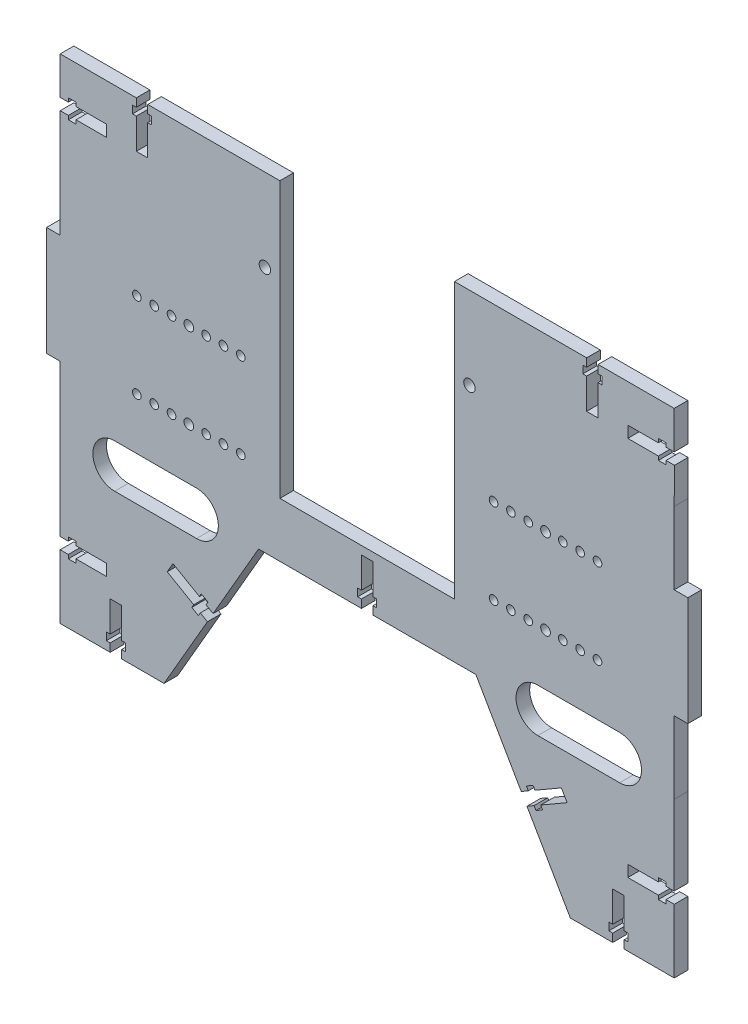
SolidWorks part; units mm, degrees
ref_plane "Front Plane" through (0, 0, 0) normal (0, 0, 1) x (1, 0, 0)
ref_plane "Top Plane" through (0, 0, 0) normal (0, 1, 0) x (1, 0, 0)
ref_plane "Right Plane" through (0, 0, 0) normal (1, 0, 0) x (0, 0, -1)
sketch "Sketch1" plane through (0, 0, 0) normal (0, 0, 1) x (1, 0, 0)
  line L0 (39.458, -28.3332) -> (72.458, -28.3332)
  line L1 (39.458, 51.6668) -> (39.458, -28.3332)
  line L2 (72.458, 51.6668) -> (39.458, 51.6668)
  line L3 (72.458, -28.3332) -> (72.458, 51.6668)
  line L4 (-73.542, -28.3332) -> (-40.542, -28.3332)
  line L5 (-73.542, 51.6668) -> (-73.542, -28.3332)
  line L6 (-40.542, 51.6668) -> (-73.542, 51.6668)
  line L7 (117.028, -95.8332) -> (117.028, -34.826)
  line L8 (117.028, -34.826) -> (112.428, -34.826)
  line L9 (107.428, -29.826) -> (107.428, 53.1596)
  line L10 (112.428, 58.1596) -> (117.0267, 58.1596)
  line L11 (117.0267, 58.1596) -> (117.0263, 74.955)
  line L12 (117.0263, 74.955) -> (117.0093, 95.0203)
  line L13 (117.0093, 95.0203) -> (36.109, 95.0203)
  line L14 (-37.1929, 95.0203) -> (-118.0932, 95.0203)
  line L15 (-118.0932, 95.0203) -> (-118.1103, 74.955)
  line L16 (-118.1103, 74.955) -> (-118.1106, 58.1596)
  line L17 (-118.1106, 58.1596) -> (-113.512, 58.1596)
  line L18 (-108.512, 53.1596) -> (-108.512, -29.826)
  line L19 (-113.512, -34.826) -> (-118.112, -34.826)
  line L20 (-118.112, -34.826) -> (-118.112, -95.8332)
  line L21 (-118.112, -95.8332) -> (-72.1334, -95.8332)
  line L22 (-72.1334, -95.8332) -> (-37.4924, -35.8332)
  line L23 (-37.4924, -35.8332) -> (36.4085, -35.8332)
  line L24 (36.4085, -35.8332) -> (71.0495, -95.8332)
  line L25 (71.0495, -95.8332) -> (117.028, -95.8332)
  line L26 (-40.542, -28.3332) -> (-40.542, 51.6668)
  circle A0 centre (-93.742, 37.1668) radius 2.5
  circle A1 centre (-93.742, -13.8332) radius 2.5
  arc A2 (107.428, -29.826) -> (112.428, -34.826) centre (112.428, -29.826) ccw
  arc A3 (112.428, 58.1596) -> (107.428, 53.1596) centre (112.428, 53.1596) ccw
  arc A4 (-37.1929, 95.0203) -> (36.109, 95.0203) centre (-0.542, 160.455) ccw
  arc A5 (-108.512, 53.1596) -> (-113.512, 58.1596) centre (-113.512, 53.1596) ccw
  arc A6 (-113.512, -34.826) -> (-108.512, -29.826) centre (-113.512, -29.826) ccw
  circle A7 centre (92.658, -13.8332) radius 2.5
  circle A8 centre (92.658, 37.1668) radius 2.5
  circle A9 centre (35.458, 29.1668) radius 2
  circle A10 centre (35.458, -5.8332) radius 2
  circle A11 centre (4.458, -5.8332) radius 2
  circle A12 centre (-5.542, -5.8332) radius 2
  circle A13 centre (-36.542, -5.8332) radius 2
  circle A14 centre (-36.542, 29.1668) radius 2
  circle A15 centre (4.458, 29.1668) radius 2
  circle A16 centre (-5.542, 29.1668) radius 2
  circle A17 centre (25.9225, 60.9906) radius 1.6
  circle A18 centre (25.9225, 81.9195) radius 1.6
  circle A19 centre (-27.0064, 81.9195) radius 1.6
  circle A20 centre (-27.0064, 60.9906) radius 1.6
extrude "Boss-Extrude1" add sketch "Sketch1" along normal blind 5
sketch "Sketch2" plane through (0, 0, 5) normal (0, 0, 1) x (1, 0, 0)
  line L4 (72.458, 51.6668) -> (39.458, 51.6668)
  line L5 (72.458, -28.3332) -> (72.458, 51.6668)
  line L6 (39.458, -28.3332) -> (72.458, -28.3332)
  line L7 (39.458, 51.6668) -> (39.458, -28.3332)
  line L8 (72.458, 51.6668) -> (39.458, 51.6668)
  line L9 (72.458, -28.3332) -> (72.458, 51.6668)
  line L10 (39.458, -28.3332) -> (72.458, -28.3332)
  line L11 (39.458, 51.6668) -> (39.458, -28.3332)
  line L12 (-40.542, 51.6668) -> (-73.542, 51.6668)
  line L13 (-40.542, -28.3332) -> (-40.542, 51.6668)
  line L14 (-73.542, -28.3332) -> (-40.542, -28.3332)
  line L15 (-73.542, 51.6668) -> (-73.542, -28.3332)
  line L16 (-40.542, 51.6668) -> (-73.542, 51.6668)
  line L17 (-40.542, -28.3332) -> (-40.542, 51.6668)
  line L18 (-73.542, -28.3332) -> (-40.542, -28.3332)
  line L19 (-73.542, 51.6668) -> (-73.542, -28.3332)
  dimension "D1" = 0
  dimension "D2" = 0
extrude "Boss-Extrude2" add sketch "Sketch2" against normal blind 5
sketch "Sketch3" plane through (0, 0, 5) normal (0, 0, 1) x (1, 0, 0)
  line L0 (31.458, 33.4416) -> (31.458, -11.5584) construction
  line L1 (8.458, -11.5584) -> (8.458, 33.4416) construction
  line L2 (-9.542, 33.4416) -> (-9.542, -11.5584) construction
  line L3 (-32.542, -11.5584) -> (-32.542, 33.4416) construction
  line L4 (31.458, 33.4416) -> (31.458, -11.5584)
  line L5 (8.458, -11.5584) -> (8.458, 33.4416)
  line L6 (-9.542, 33.4416) -> (-9.542, -11.5584)
  line L7 (-32.542, -11.5584) -> (-32.542, 33.4416)
  line L8 (-32.542, -11.5584) -> (-9.542, -11.5584)
  line L9 (-32.542, 33.4416) -> (-9.542, 33.4416)
  line L10 (8.458, 33.4416) -> (31.458, 33.4416)
  line L11 (8.458, -11.5584) -> (31.458, -11.5584)
extrude "Cut-Extrude3" cut sketch "Sketch3" against normal blind 5
sketch "Sketch4" plane through (0, 0, 5) normal (0, 0, 1) x (1, 0, 0)
  circle A1 centre (92.658, -13.8332) radius 2.5
  circle A2 centre (92.658, -13.8332) radius 2.5
  circle A3 centre (92.658, 37.1668) radius 2.5
  circle A4 centre (92.658, 37.1668) radius 2.5
  circle A5 centre (35.458, -5.8332) radius 2
  circle A6 centre (35.458, -5.8332) radius 2
  circle A7 centre (35.458, 29.1668) radius 2
  circle A8 centre (35.458, 29.1668) radius 2
  circle A9 centre (4.458, -5.8332) radius 2
  circle A10 centre (4.458, -5.8332) radius 2
  circle A11 centre (4.458, 29.1668) radius 2
  circle A12 centre (4.458, 29.1668) radius 2
  circle A13 centre (-5.542, -5.8332) radius 2
  circle A14 centre (-5.542, -5.8332) radius 2
  circle A15 centre (-5.542, 29.1668) radius 2
  circle A16 centre (-5.542, 29.1668) radius 2
  circle A17 centre (-36.542, -5.8332) radius 2
  circle A18 centre (-36.542, -5.8332) radius 2
  circle A19 centre (-36.542, 29.1668) radius 2
  circle A20 centre (-36.542, 29.1668) radius 2
  circle A21 centre (-93.742, -13.8332) radius 2.5
  circle A22 centre (-93.742, -13.8332) radius 2.5
  circle A23 centre (-93.742, 37.1668) radius 2.5
  circle A24 centre (-93.742, 37.1668) radius 2.5
  circle A25 centre (25.9225, 60.9906) radius 1.6
  circle A26 centre (25.9225, 60.9906) radius 1.6
  circle A27 centre (25.9225, 81.9195) radius 1.6
  circle A28 centre (25.9225, 81.9195) radius 1.6
  circle A29 centre (-27.0064, 81.9195) radius 1.6
  circle A30 centre (-27.0064, 81.9195) radius 1.6
  circle A31 centre (-27.0064, 60.9906) radius 1.6
  circle A32 centre (-27.0064, 60.9906) radius 1.6
  dimension "D1" = 0
  dimension "D2" = 0
  dimension "D3" = 0
  dimension "D4" = 0
  dimension "D5" = 0
  dimension "D6" = 0
  dimension "D7" = 0
  dimension "D8" = 0
  dimension "D9" = 0
  dimension "D10" = 0
  dimension "D11" = 0
  dimension "D12" = 0
  dimension "D13" = 0
  dimension "D14" = 0
  dimension "D15" = 0
  dimension "D16" = 0
extrude "Boss-Extrude3" add sketch "Sketch4" against normal blind 5
sketch "Sketch5" plane through (0, 0, 5) normal (0, 0, 1) x (1, 0, 0)
  line L0 (-92.842, 10.9401) -> (-51.8932, 10.9401) construction
  line L1 (-92.842, 14.0401) -> (-92.842, 7.8401) construction
  line L2 (-0.542, -35.8332) -> (-0.542, 25.4222) construction
  line L3 (-37.4924, -35.8332) -> (36.4085, -35.8332) construction
  line L4 (91.758, 10.9401) -> (50.8093, 10.9401) construction
  circle A0 centre (-84.9795, 26.5626) radius 1.5875
  circle A1 centre (-78.6295, 26.5626) radius 1.5875
  circle A2 centre (-72.2795, 26.5626) radius 1.5875
  circle A3 centre (-65.9295, 26.5626) radius 1.7775
  circle A4 centre (-59.5795, 26.5626) radius 1.5875
  circle A5 centre (-53.2295, 26.5626) radius 1.5875
  circle A6 centre (-46.8795, 26.5626) radius 1.5875
  circle A7 centre (-46.8795, -4.6823) radius 1.5875
  circle A8 centre (-53.2295, -4.6823) radius 1.5875
  circle A9 centre (-59.5795, -4.6823) radius 1.5875
  circle A10 centre (-65.9295, -4.6823) radius 1.7775
  circle A11 centre (-72.2795, -4.6823) radius 1.5875
  circle A12 centre (-78.6295, -4.6823) radius 1.5875
  circle A13 centre (-84.9795, -4.6823) radius 1.5875
  circle A14 centre (83.8955, -4.6823) radius 1.5875
  circle A15 centre (77.5455, -4.6823) radius 1.5875
  circle A16 centre (71.1955, -4.6823) radius 1.5875
  circle A17 centre (64.8455, -4.6823) radius 1.7775
  circle A18 centre (58.4955, -4.6823) radius 1.5875
  circle A19 centre (52.1455, -4.6823) radius 1.5875
  circle A20 centre (45.7955, -4.6823) radius 1.5875
  circle A21 centre (45.7955, 26.5626) radius 1.5875
  circle A22 centre (52.1455, 26.5626) radius 1.5875
  circle A23 centre (58.4955, 26.5626) radius 1.5875
  circle A24 centre (64.8455, 26.5626) radius 1.7775
  circle A25 centre (71.1955, 26.5626) radius 1.5875
  circle A26 centre (77.5455, 26.5626) radius 1.5875
  circle A27 centre (83.8955, 26.5626) radius 1.5875
extrude "Cut-Extrude4" cut sketch "Sketch5" against normal blind 5
sketch "Sketch7" plane through (0, 0, 5) normal (0, 0, 1) x (1, 0, 0)
  line L2 (-37.1929, 89.2951) -> (-75.5429, 89.2951) construction
  line L7 (36.109, 89.2951) -> (74.459, 89.2951) construction
  line L9 (112.028, -35.5484) -> (112.028, -63.9534) construction
  line L10 (-113.112, -35.5484) -> (-113.112, -63.9534) construction
  line L15 (112.028, -91.5584) -> (93.683, -91.5584) construction
  line L18 (73.2366, -90.3465) -> (58.0376, -64.0211) construction
  line L23 (-37.4915, -31.5584) -> (-2.6415, -31.5584) construction
  line L24 (-74.3205, -90.3465) -> (-59.1215, -64.0211) construction
  line L25 (-113.112, -91.5584) -> (-94.767, -91.5584) construction
  line L27 (-113.0929, 89.2951) -> (-113.0929, 75.4651)
  line L29 (-37.1929, 89.2951) -> (-113.0929, 89.2951)
  line L30 (36.109, 89.2951) -> (112.0089, 89.2951)
  line L31 (112.0089, 89.2951) -> (112.009, 75.4651)
  line L32 (112.028, -35.5484) -> (112.028, -91.5584)
  line L33 (-113.112, -35.5484) -> (-113.112, -91.5584)
  line L34 (112.028, -91.5584) -> (73.9362, -91.5584)
  line L35 (73.2366, -90.3465) -> (58.0376, -64.0211)
  line L36 (-37.4915, -31.5584) -> (-2.6415, -31.5584)
  line L37 (-74.3205, -90.3465) -> (-59.1215, -64.0211)
  line L38 (-113.112, -91.5584) -> (-75.0201, -91.5584)
  line L39 (-74.3205, -90.3465) -> (-75.0201, -91.5584)
  line L40 (-37.4915, -31.5584) -> (-40.3791, -31.5584)
  line L41 (-59.1215, -64.0211) -> (-40.3791, -31.5584)
  line L42 (-113.112, -35.5484) -> (-118.112, -34.826)
  line L43 (-118.112, -34.826) -> (-118.112, -95.8332)
  line L44 (-118.112, -95.8332) -> (-72.1334, -95.8332)
  line L45 (-72.1334, -95.8332) -> (-37.4924, -35.8332)
  line L46 (-37.4924, -35.8332) -> (36.4085, -35.8332)
  line L47 (36.4085, -35.8332) -> (71.0495, -95.8332)
  line L48 (71.0495, -95.8332) -> (117.028, -95.8332)
  line L49 (117.028, -95.8332) -> (117.028, -34.826)
  line L50 (117.028, -34.826) -> (112.028, -35.5484)
  line L51 (-2.6415, -31.5584) -> (39.2952, -31.5584)
  line L52 (58.0376, -64.0211) -> (39.2952, -31.5584)
  line L53 (73.2366, -90.3465) -> (73.9362, -91.5584)
  line L54 (117.0267, 58.1596) -> (117.0263, 74.955) construction
  line L55 (117.0263, 74.955) -> (117.0093, 95.0203) construction
  line L56 (117.0093, 95.0203) -> (36.109, 95.0203) construction
  line L57 (-118.1106, 58.1596) -> (-113.512, 58.1596) construction
  line L58 (-118.1103, 74.955) -> (-118.1106, 58.1596) construction
  line L59 (-118.0932, 95.0203) -> (-118.1103, 74.955) construction
  line L60 (-37.1929, 95.0203) -> (-118.0932, 95.0203) construction
  line L61 (117.0267, 58.1596) -> (117.0263, 74.955)
  line L62 (117.0263, 74.955) -> (117.0093, 95.0203)
  line L63 (117.0093, 95.0203) -> (36.109, 95.0203)
  line L64 (-118.1106, 58.1596) -> (-113.512, 58.1596)
  line L65 (-118.1103, 74.955) -> (-118.1106, 58.1596)
  line L66 (-118.0932, 95.0203) -> (-118.1103, 74.955)
  line L67 (-37.1929, 95.0203) -> (-118.0932, 95.0203)
  line L68 (-37.1929, 95.0203) -> (-37.1929, 89.2951)
  line L69 (36.109, 95.0203) -> (36.109, 89.2951)
  line L70 (-113.512, 58.1596) -> (-113.0929, 75.4651)
  line L71 (117.0267, 58.1596) -> (112.009, 75.4651)
extrude "Cut-Extrude5" cut sketch "Sketch7" against normal blind 10
sketch "Sketch9" plane through (0, 0, 5) normal (0, 0, 1) x (1, 0, 0)
  line L0 (-92.667, -96.5584) -> (-92.667, -68.7145) construction
  line L1 (-97.667, -96.5584) -> (-87.667, -96.5584) construction
  line L2 (-118.112, -66.0534) -> (-90.5831, -66.0534) construction
  line L3 (-118.112, -61.0534) -> (-118.112, -71.0534) construction
  line L4 (-53.7414, -64.7025) -> (-78.8211, -50.2227) construction
  line L5 (-56.2414, -69.0326) -> (-51.2414, -60.3723) construction
  line L6 (-107.2929, 71.2651) -> (-96.0929, 71.2651)
  line L8 (-107.2929, 69.8651) -> (-107.2929, 71.2651)
  line L21 (-110.0929, 69.8651) -> (-107.2929, 69.8651)
  line L34 (-110.0929, 71.2651) -> (-110.0929, 69.8651)
  line L47 (-113.0929, 71.2651) -> (-110.0929, 71.2651)
  line L60 (-77.6429, 89.2951) -> (-79.7429, 89.2951)
  line L65 (-113.0929, 89.2951) -> (-37.1929, 89.2951) construction
  line L78 (-79.7429, 89.2951) -> (-79.7429, 86.2951)
  line L90 (-0.5415, -36.5584) -> (-0.5415, -3.9222) construction
  line L91 (-5.5415, -36.5584) -> (4.4585, -36.5584) construction
  line L92 (-118.0929, 73.3651) -> (-88.4214, 73.3651) construction
  line L94 (-77.6429, 94.2951) -> (-77.6429, 80.7077) construction
  line L159 (-79.7429, 86.2951) -> (-81.1429, 86.2951)
  line L160 (-90.567, -91.5584) -> (-94.767, -91.5584)
  line L161 (-81.1429, 86.2951) -> (-81.1429, 83.4951)
  line L162 (-75.0201, -91.5584) -> (-113.112, -91.5584) construction
  line L163 (-94.767, -91.5584) -> (-94.767, -88.5584)
  line L164 (-94.767, -88.5584) -> (-96.167, -88.5584)
  line L165 (-96.167, -88.5584) -> (-96.167, -85.7584)
  line L166 (-96.167, -85.7584) -> (-94.767, -85.7584)
  line L167 (-94.767, -85.7584) -> (-94.767, -74.5584)
  line L168 (-94.767, -74.5584) -> (-90.567, -74.5584)
  line L169 (-113.112, -68.1534) -> (-113.112, -63.9534)
  line L170 (-113.112, -91.5584) -> (-113.112, -35.5484) construction
  line L171 (-113.112, -63.9534) -> (-110.112, -63.9534)
  line L172 (-110.112, -63.9534) -> (-110.112, -62.5534)
  line L173 (-110.112, -62.5534) -> (-107.312, -62.5534)
  line L174 (-107.312, -62.5534) -> (-107.312, -63.9534)
  line L175 (-107.312, -63.9534) -> (-96.112, -63.9534)
  line L176 (-96.112, -63.9534) -> (-96.112, -68.1534)
  line L177 (-57.0215, -60.3838) -> (-59.1215, -64.0211)
  line L178 (-40.3791, -31.5584) -> (-75.0201, -91.5584) construction
  line L179 (-59.1215, -64.0211) -> (-61.7196, -62.5211)
  line L180 (-61.7196, -62.5211) -> (-62.4196, -63.7335)
  line L181 (-62.4196, -63.7335) -> (-64.8444, -62.3335)
  line L182 (-64.8444, -62.3335) -> (-64.1444, -61.1211)
  line L183 (-64.1444, -61.1211) -> (-73.8439, -55.5211)
  line L184 (-73.8439, -55.5211) -> (-71.7439, -51.8838)
  line L185 (-107.312, -68.1534) -> (-96.112, -68.1534)
  line L186 (-107.312, -69.5534) -> (-107.312, -68.1534)
  line L187 (-110.112, -69.5534) -> (-107.312, -69.5534)
  line L188 (-110.112, -68.1534) -> (-110.112, -69.5534)
  line L189 (-113.112, -68.1534) -> (-110.112, -68.1534)
  line L190 (-90.567, -85.7584) -> (-90.567, -74.5584)
  line L191 (-89.167, -85.7584) -> (-90.567, -85.7584)
  line L192 (-89.167, -88.5584) -> (-89.167, -85.7584)
  line L193 (-90.567, -88.5584) -> (-89.167, -88.5584)
  line L194 (-90.567, -91.5584) -> (-90.567, -88.5584)
  line L195 (-62.0444, -57.4838) -> (-71.7439, -51.8838)
  line L196 (-61.3444, -56.2714) -> (-62.0444, -57.4838)
  line L197 (-58.9196, -57.6714) -> (-61.3444, -56.2714)
  line L198 (-59.6196, -58.8838) -> (-58.9196, -57.6714)
  line L199 (-57.0215, -60.3838) -> (-59.6196, -58.8838)
  line L202 (-113.0929, 75.4651) -> (-110.0929, 75.4651)
  line L203 (-110.0929, 75.4651) -> (-110.0929, 76.8651)
  line L204 (-110.0929, 76.8651) -> (-107.2929, 76.8651)
  line L205 (-107.2929, 76.8651) -> (-107.2929, 75.4651)
  line L206 (-107.2929, 75.4651) -> (-96.0929, 75.4651)
  line L207 (-96.0929, 75.4651) -> (-96.0929, 71.2651)
  line L208 (-81.1429, 83.4951) -> (-79.7429, 83.4951)
  line L209 (-79.7429, 83.4951) -> (-79.7429, 72.2951)
  line L210 (-79.7429, 72.2951) -> (-75.5429, 72.2951)
  line L211 (-75.5429, 83.4951) -> (-75.5429, 72.2951)
  line L212 (-74.1429, 83.4951) -> (-75.5429, 83.4951)
  line L213 (-74.1429, 86.2951) -> (-74.1429, 83.4951)
  line L214 (-75.5429, 86.2951) -> (-74.1429, 86.2951)
  line L215 (-75.5429, 89.2951) -> (-75.5429, 86.2951)
  line L216 (-77.6429, 89.2951) -> (-75.5429, 89.2951)
  line L217 (76.5598, 94.2951) -> (76.5598, 80.7077) construction
  line L218 (117.0098, 73.3651) -> (87.3384, 73.3651) construction
  line L219 (52.6583, -64.7025) -> (77.738, -50.2227) construction
  line L220 (117.0289, -66.0534) -> (89.5, -66.0534) construction
  line L221 (91.5839, -96.5584) -> (91.5839, -68.7145) construction
  line L222 (76.5598, 89.2951) -> (74.4598, 89.2951)
  line L223 (74.4598, 89.2951) -> (74.4598, 86.2951)
  line L224 (74.4598, 86.2951) -> (73.0598, 86.2951)
  line L225 (73.0598, 86.2951) -> (73.0598, 83.4951)
  line L226 (73.0598, 83.4951) -> (74.4598, 83.4951)
  line L227 (74.4598, 83.4951) -> (74.4598, 72.2951)
  line L228 (78.6598, 72.2951) -> (74.4598, 72.2951)
  line L229 (78.6598, 83.4951) -> (78.6598, 72.2951)
  line L230 (80.0598, 83.4951) -> (78.6598, 83.4951)
  line L231 (95.0098, 75.4651) -> (95.0098, 71.2651)
  line L232 (106.2098, 75.4651) -> (95.0098, 75.4651)
  line L233 (106.2098, 76.8651) -> (106.2098, 75.4651)
  line L234 (109.0098, 76.8651) -> (106.2098, 76.8651)
  line L235 (109.0098, 75.4651) -> (109.0098, 76.8651)
  line L236 (112.0098, 75.4651) -> (109.0098, 75.4651)
  line L237 (112.0098, 75.4622) -> (112.0098, 75.4651)
  line L238 (55.9384, -60.3838) -> (58.5365, -58.8838)
  line L239 (58.5365, -58.8838) -> (57.8365, -57.6714)
  line L240 (57.8365, -57.6714) -> (60.2614, -56.2714)
  line L241 (60.2614, -56.2714) -> (60.9614, -57.4838)
  line L242 (60.9614, -57.4838) -> (70.6609, -51.8838)
  line L243 (89.4839, -91.5584) -> (89.4839, -88.5584)
  line L244 (89.4839, -88.5584) -> (88.0839, -88.5584)
  line L245 (88.0839, -88.5584) -> (88.0839, -85.7584)
  line L246 (88.0839, -85.7584) -> (89.4839, -85.7584)
  line L247 (89.4839, -85.7584) -> (89.4839, -74.5584)
  line L248 (112.0289, -68.1534) -> (109.0289, -68.1534)
  line L249 (109.0289, -68.1534) -> (109.0289, -69.5534)
  line L250 (109.0289, -69.5534) -> (106.2289, -69.5534)
  line L251 (106.2289, -69.5534) -> (106.2289, -68.1534)
  line L252 (106.2289, -68.1534) -> (95.0289, -68.1534)
  line L253 (72.7609, -55.5211) -> (70.6609, -51.8838)
  line L254 (63.0614, -61.1211) -> (72.7609, -55.5211)
  line L255 (63.7614, -62.3335) -> (63.0614, -61.1211)
  line L256 (61.3365, -63.7335) -> (63.7614, -62.3335)
  line L257 (60.6365, -62.5211) -> (61.3365, -63.7335)
  line L258 (58.0384, -64.0211) -> (60.6365, -62.5211)
  line L259 (55.9384, -60.3838) -> (58.0384, -64.0211)
  line L260 (95.0289, -63.9534) -> (95.0289, -68.1534)
  line L261 (106.2289, -63.9534) -> (95.0289, -63.9534)
  line L262 (106.2289, -62.5534) -> (106.2289, -63.9534)
  line L263 (109.0289, -62.5534) -> (106.2289, -62.5534)
  line L264 (109.0289, -63.9534) -> (109.0289, -62.5534)
  line L265 (112.0289, -63.9534) -> (109.0289, -63.9534)
  line L266 (112.0289, -68.1534) -> (112.0289, -63.9534)
  line L267 (93.6839, -74.5584) -> (89.4839, -74.5584)
  line L268 (93.6839, -85.7584) -> (93.6839, -74.5584)
  line L269 (95.0839, -85.7584) -> (93.6839, -85.7584)
  line L270 (95.0839, -88.5584) -> (95.0839, -85.7584)
  line L271 (93.6839, -88.5584) -> (95.0839, -88.5584)
  line L272 (93.6839, -91.5584) -> (93.6839, -88.5584)
  line L273 (80.0598, 86.2951) -> (80.0598, 83.4951)
  line L274 (89.4839, -91.5584) -> (93.6839, -91.5584)
  line L275 (78.6598, 86.2951) -> (80.0598, 86.2951)
  line L276 (78.6598, 89.2951) -> (78.6598, 86.2951)
  line L277 (76.5598, 89.2951) -> (78.6598, 89.2951)
  line L278 (112.0098, 71.2651) -> (109.0098, 71.2651)
  line L279 (109.0098, 71.2651) -> (109.0098, 69.8651)
  line L280 (109.0098, 69.8651) -> (106.2098, 69.8651)
  line L281 (106.2098, 69.8651) -> (106.2098, 71.2651)
  line L282 (106.2098, 71.2651) -> (95.0098, 71.2651)
  line L283 (117.028, -34.826) -> (112.028, -35.5484) construction
  line L284 (117.028, -34.826) -> (112.428, -34.826) construction
  line L285 (117.028, -34.826) -> (112.028, -35.5484)
  line L286 (117.028, -34.826) -> (112.428, -34.826)
  line L287 (112.028, -35.5484) -> (112.028, -34.81)
  line L288 (-113.1111, -35.5484) -> (-113.1111, -34.81)
  line L289 (-118.1111, -34.826) -> (-113.5111, -34.826)
  line L290 (-118.1111, -34.826) -> (-113.1111, -35.5484)
  line L291 (-113.0929, 71.2651) -> (-113.0929, 58.142)
  line L294 (-113.512, 58.1596) -> (-113.0929, 75.4651)
  line L295 (-113.0929, 71.2651) -> (-113.1946, 71.2651)
  line L296 (-113.0929, 73.3651) -> (-113.1437, 73.3651)
  line L297 (117.0098, 73.3651) -> (87.3384, 73.3651) construction
  line L298 (112.0098, 73.3651) -> (112.0607, 73.3651)
  line L299 (112.0098, 71.2651) -> (112.1115, 71.2651)
  line L300 (112.0098, 71.2651) -> (112.0098, 58.142)
  line L301 (112.0098, 71.2651) -> (109.0098, 71.2651)
  line L302 (109.0098, 71.2651) -> (109.0098, 69.8651)
  line L303 (109.0098, 69.8651) -> (106.2098, 69.8651)
  line L304 (106.2098, 69.8651) -> (106.2098, 71.2651)
  line L305 (106.2098, 71.2651) -> (95.0098, 71.2651)
  line L306 (-2.6415, -31.5584) -> (-2.6415, -28.5584)
  line L307 (39.2952, -31.5584) -> (-40.3791, -31.5584) construction
  line L308 (-2.6415, -28.5584) -> (-4.0415, -28.5584)
  line L309 (-4.0415, -28.5584) -> (-4.0415, -25.7584)
  line L310 (-4.0415, -25.7584) -> (-2.6415, -25.7584)
  line L311 (-2.6415, -25.7584) -> (-2.6415, -14.5584)
  line L312 (-2.6415, -14.5584) -> (1.5585, -14.5584)
  line L313 (-2.6415, -31.5584) -> (-0.542, -31.5584)
  line L314 (1.5585, -31.5584) -> (-0.5411, -31.5584)
  line L315 (1.5585, -25.7584) -> (1.5585, -14.5584)
  line L316 (2.9585, -25.7584) -> (1.5585, -25.7584)
  line L317 (2.9585, -28.5584) -> (2.9585, -25.7584)
  line L318 (1.5585, -28.5584) -> (2.9585, -28.5584)
  line L319 (1.5585, -31.5584) -> (1.5585, -28.5584)
  line L320 (112.009, 75.4651) -> (117.0267, 58.1596) construction
  line L321 (112.428, 58.1596) -> (117.0267, 58.1596) construction
  line L322 (112.009, 75.4651) -> (117.0267, 58.1596)
  line L323 (112.428, 58.1596) -> (117.0267, 58.1596)
  line L324 (112.0098, 58.142) -> (112.1115, 71.2651)
  arc A0 (107.428, -29.826) -> (112.428, -34.826) centre (112.428, -29.826) ccw construction
  arc A1 (112.028, -34.81) -> (112.428, -34.826) centre (112.428, -29.826) ccw
  arc A2 (-113.1111, -34.81) -> (-113.5111, -34.826) centre (-113.5111, -29.826) cw
  arc A3 (-108.512, 53.1596) -> (-113.512, 58.1596) centre (-113.512, 53.1596) ccw construction
  arc A4 (-113.0929, 58.142) -> (-113.512, 58.1596) centre (-113.512, 53.1596) ccw
  arc A5 (112.0098, 58.142) -> (112.4289, 58.1596) centre (112.4289, 53.1596) cw
  point P8 (-96.0929, 73.3651)
  point P60 (-96.112, -66.0534)
  point P65 (-113.112, -66.0534)
  point P66 (-92.667, -74.5584)
  point P71 (-92.667, -91.5584)
  point P72 (-72.7939, -53.7025)
  point P77 (-58.0715, -62.2025)
  point P88 (-113.0929, 73.3651)
  point P99 (-77.6429, 72.2951)
  point P175 (76.5598, 72.2951)
  point P176 (112.0098, 73.3651)
  point P177 (56.9884, -62.2025)
  point P178 (71.7109, -53.7025)
  point P179 (91.5839, -91.5584)
  point P180 (91.5839, -74.5584)
  point P181 (112.0289, -66.0534)
  point P182 (95.0289, -66.0534)
  point P183 (95.0098, 73.3651)
  point P211 (112.0098, 73.3651)
  point P230 (-0.5415, -14.5584)
  dimension "D1" = 2.1
  dimension "D2" = 2.1
  dimension "D3" = 3.5
  dimension "D4" = 2.8
  dimension "D5" = 3
  dimension "D6" = 17
  dimension "D7" = 4.2
  dimension "D8" = 4.2
  dimension "D9" = 7
  dimension "D10" = 17
  dimension "D11" = 2.8
  dimension "D12" = 3
  dimension "D13" = 3
  dimension "D14" = 2.1
  dimension "D15" = 2.1
  dimension "D16" = 3.5
  dimension "D17" = 2.8
  dimension "D18" = 17
  dimension "D20" = 2.1
  dimension "D21" = 3.5
  dimension "D23" = 2.8
  dimension "D24" = 4.2
  dimension "D25" = 2.1
  dimension "D26" = 3.5
  dimension "D27" = 2.8
  dimension "D28" = 3
  dimension "D29" = 4.2
  dimension "D30" = 17
  dimension "D31" = 4.2
  dimension "D32" = 7
  dimension "D33" = 2.8
  dimension "D34" = 17
  dimension "D35" = 3
extrude "Cut-Extrude9" cut sketch "Sketch9" against normal blind 10
sketch "Sketch13" plane through (0, 0, 5) normal (0, 0, 1) x (1, 0, 0)
  line L0 (-0.5415, -36.5584) -> (-0.5415, -10.9123) construction
  line L1 (-5.5415, -36.5584) -> (4.4585, -36.5584) construction
  line L2 (1.5585, -31.5584) -> (-2.6415, -31.5584)
  line L3 (39.2952, -31.5584) -> (-40.3791, -31.5584) construction
  line L4 (-2.6415, -31.5584) -> (-2.6415, -28.5584)
  line L5 (-2.6415, -28.5584) -> (-4.0415, -28.5584)
  line L6 (-4.0415, -28.5584) -> (-4.0415, -25.7584)
  line L7 (-4.0415, -25.7584) -> (-2.6415, -25.7584)
  line L8 (-2.6415, -25.7584) -> (-2.6415, -14.5584)
  line L9 (-2.6415, -14.5584) -> (1.5585, -14.5584)
  line L10 (1.5585, -25.7584) -> (1.5585, -14.5584)
  line L11 (2.9585, -25.7584) -> (1.5585, -25.7584)
  line L12 (2.9585, -28.5584) -> (2.9585, -25.7584)
  line L13 (1.5585, -28.5584) -> (2.9585, -28.5584)
  line L14 (1.5585, -31.5584) -> (1.5585, -28.5584)
  point P16 (-0.5415, -14.5584)
  point P21 (-0.5415, -31.5584)
  dimension "D1" = 2.1
  dimension "D2" = 3.5
  dimension "D3" = 4.2
  dimension "D4" = 2.8
  dimension "D5" = 3
  dimension "D6" = 17
extrude "Cut-Extrude10" cut sketch "Sketch13" against normal blind 10
sketch "Sketch14" plane through (15.8069, 9.1261, 0) normal (0.866, 0.5, 0) x (0, 0, -1)
  line L4 (0, -80.2631) -> (-5, -80.2631)
  line L5 (-5, -80.2631) -> (-5, -84.4631)
  line L6 (-5, -84.4631) -> (0, -84.4631)
  line L7 (0, -84.4631) -> (0, -80.2631)
  line L8 (0, -80.2631) -> (-5, -80.2631)
  line L9 (-5, -80.2631) -> (-5, -84.4631)
  line L10 (-5, -84.4631) -> (0, -84.4631)
  line L11 (0, -84.4631) -> (0, -80.2631)
  dimension "D1" = 0
extrude "Cut-Extrude11" cut sketch "Sketch14" against normal blind 10
sketch "Sketch16" plane through (0, 0, 5) normal (0, 0, 1) x (1, 0, 0)
  line L0 (-113.112, -35.5484) -> (-113.112, -34.81)
  line L1 (-113.112, -35.5484) -> (-118.112, -34.826) construction
  line L2 (-113.512, -34.826) -> (-118.112, -34.826) construction
  line L3 (-113.112, -35.5484) -> (-118.112, -34.826)
  line L4 (-113.512, -34.826) -> (-118.112, -34.826)
  line L6 (112.028, -35.5484) -> (119.0204, -35.5484)
  line L7 (112.028, -35.5484) -> (112.028, -32.2288)
  line L8 (112.028, -32.2288) -> (119.0204, -32.2288)
  line L9 (119.0204, -35.5484) -> (119.0204, -32.2288)
  arc A0 (-113.512, -34.826) -> (-108.512, -29.826) centre (-113.512, -29.826) ccw construction
  arc A1 (-113.512, -34.826) -> (-113.112, -34.81) centre (-113.512, -29.826) ccw
extrude "Cut-Extrude13" cut sketch "Sketch16" against normal blind 5
sketch "Sketch17" plane through (0, 0, 5) normal (0, 0, 1) x (1, 0, 0)
  line L0 (-32.542, 89.2951) -> (-45.8022, 89.2951)
  line L5 (36.109, 89.2951) -> (31.5176, 89.2951)
  line L6 (-32.542, 33.4416) -> (31.5176, 33.4416)
  line L11 (-32.542, 33.4416) -> (-32.542, 89.2951)
  line L16 (31.5176, 33.4416) -> (31.5176, 89.2951)
  line L17 (-32.542, 33.4416) -> (31.5176, 91.7976) construction
  line L19 (-32.542, 91.7976) -> (31.5176, 33.4416) construction
  line L20 (-9.542, -11.5584) -> (8.458, -11.5584)
  line L21 (-9.542, -11.5584) -> (-9.542, 33.4416)
  line L22 (-9.542, 33.4416) -> (8.458, 33.4416)
  line L23 (8.458, -11.5584) -> (8.458, 33.4416)
  line L24 (-9.542, -11.5584) -> (8.458, 33.4416) construction
  line L25 (-9.542, 33.4416) -> (8.458, -11.5584) construction
  line L26 (36.109, 89.2951) -> (36.109, 123.2498)
  line L27 (36.109, 123.2498) -> (-45.8022, 123.2498)
  line L28 (-45.8022, 89.2951) -> (-45.8022, 123.2498)
  line L29 (36.109, 89.2951) -> (-45.8022, 123.2498) construction
  line L30 (36.109, 123.2498) -> (-45.8022, 89.2951) construction
  point P4 (-0.5122, 62.6196)
  point P11 (-0.542, 10.9416)
  point P14 (-4.8466, 106.2724)
extrude "Cut-Extrude14" cut sketch "Sketch17" against normal blind 5
sketch "Sketch18" plane through (31.458, 0, 0) normal (-1, 0, 0) x (0, 0, 1)
  line L0 (0, 89.2951) -> (5, 89.2951) construction
  line L1 (5, -11.5584) -> (0, -11.5584)
  line L2 (5, -11.5584) -> (5, 89.2951)
  line L3 (5, 89.2951) -> (0, 89.2951)
  line L4 (0, -11.5584) -> (0, 89.2951)
extrude "Boss-Extrude4" add sketch "Sketch18" against normal blind 9
sketch "Sketch19" plane through (0, 0, 5) normal (0, 0, 1) x (1, 0, 0)
  line L0 (34.458, 54.0826) -> (34.458, 64.0826) construction
  line L1 (34.458, 54.0826) -> (34.458, 64.0826) construction
  line L2 (34.458, 59.0826) -> (39.458, 59.0826) construction
  line L3 (-0.542, -11.5584) -> (-0.542, 28.7081) construction
  line L4 (-32.542, -11.5584) -> (31.458, -11.5584) construction
  line L5 (-35.542, 59.0826) -> (-40.542, 59.0826) construction
  line L6 (-35.542, 54.0826) -> (-35.542, 64.0826) construction
  circle A0 centre (36.958, 59.0826) radius 2.1
  circle A1 centre (-38.042, 59.0826) radius 2.1
  dimension "D2" = 4.2
  dimension "D1" = 5
extrude "Cut-Extrude15" cut sketch "Sketch19" against normal blind 5
sketch "Sketch20" plane through (0, 0, 5) normal (0, 0, 1) x (1, 0, 0)
  line L0 (-74.1429, 83.4951) -> (-75.5429, 83.4951) construction
  line L1 (-74.1429, 86.2951) -> (-74.1429, 83.4951) construction
  line L2 (-75.5429, 86.2951) -> (-74.1429, 86.2951) construction
  line L3 (-75.5429, 89.2951) -> (-75.5429, 86.2951) construction
  line L4 (-79.7429, 89.2951) -> (-79.7429, 86.2951) construction
  line L5 (-79.7429, 86.2951) -> (-81.1429, 86.2951) construction
  line L6 (-81.1429, 86.2951) -> (-81.1429, 83.4951) construction
  line L7 (-81.1429, 83.4951) -> (-79.7429, 83.4951) construction
  line L8 (-79.7429, 83.4951) -> (-79.7429, 72.2951) construction
  line L9 (-79.7429, 72.2951) -> (-75.5429, 72.2951) construction
  line L10 (-75.5429, 83.4951) -> (-75.5429, 72.2951) construction
  line L11 (74.4598, 89.2951) -> (74.4598, 86.2951) construction
  line L12 (74.4598, 86.2951) -> (73.0598, 86.2951) construction
  line L13 (73.0598, 86.2951) -> (73.0598, 83.4951) construction
  line L14 (73.0598, 83.4951) -> (74.4598, 83.4951) construction
  line L15 (74.4598, 83.4951) -> (74.4598, 72.2951) construction
  line L16 (78.6598, 72.2951) -> (74.4598, 72.2951) construction
  line L17 (78.6598, 83.4951) -> (78.6598, 72.2951) construction
  line L18 (80.0598, 83.4951) -> (78.6598, 83.4951) construction
  line L19 (80.0598, 86.2951) -> (80.0598, 83.4951) construction
  line L20 (78.6598, 86.2951) -> (80.0598, 86.2951) construction
  line L21 (78.6598, 89.2951) -> (78.6598, 86.2951) construction
  line L22 (-74.1429, 83.4951) -> (-75.5429, 83.4951)
  line L23 (-74.1429, 86.2951) -> (-74.1429, 83.4951)
  line L24 (-75.5429, 86.2951) -> (-74.1429, 86.2951)
  line L25 (-75.5429, 89.2951) -> (-75.5429, 86.2951)
  line L26 (-79.7429, 89.2951) -> (-79.7429, 86.2951)
  line L27 (-79.7429, 86.2951) -> (-81.1429, 86.2951)
  line L28 (-81.1429, 86.2951) -> (-81.1429, 83.4951)
  line L29 (-81.1429, 83.4951) -> (-79.7429, 83.4951)
  line L30 (-79.7429, 83.4951) -> (-79.7429, 72.2951)
  line L31 (-79.7429, 72.2951) -> (-75.5429, 72.2951)
  line L32 (-75.5429, 83.4951) -> (-75.5429, 72.2951)
  line L33 (74.4598, 89.2951) -> (74.4598, 86.2951)
  line L34 (74.4598, 86.2951) -> (73.0598, 86.2951)
  line L35 (73.0598, 86.2951) -> (73.0598, 83.4951)
  line L36 (73.0598, 83.4951) -> (74.4598, 83.4951)
  line L37 (74.4598, 83.4951) -> (74.4598, 72.2951)
  line L38 (78.6598, 72.2951) -> (74.4598, 72.2951)
  line L39 (78.6598, 83.4951) -> (78.6598, 72.2951)
  line L40 (80.0598, 83.4951) -> (78.6598, 83.4951)
  line L41 (80.0598, 86.2951) -> (80.0598, 83.4951)
  line L42 (78.6598, 86.2951) -> (80.0598, 86.2951)
  line L43 (78.6598, 89.2951) -> (78.6598, 86.2951)
  line L44 (-113.112, -34.81) -> (-113.0929, 58.142)
  line L45 (112.028, -34.81) -> (112.0098, 58.1421)
  line L46 (-108.512, 53.1596) -> (-108.512, -29.826) construction
  line L47 (107.428, -29.826) -> (107.428, 53.1596) construction
  line L48 (-108.512, 53.1596) -> (-108.512, -29.826)
  line L49 (107.428, -29.826) -> (107.428, 53.1596)
  line L50 (78.6598, 89.2951) -> (74.4598, 89.2951)
  line L51 (-75.5429, 89.2951) -> (-79.7429, 89.2951)
  arc A0 (-113.112, -34.81) -> (-108.512, -29.826) centre (-113.512, -29.826) ccw construction
  arc A1 (-108.512, 53.1596) -> (-113.0929, 58.142) centre (-113.512, 53.1596) ccw construction
  arc A2 (112.0098, 58.1421) -> (107.428, 53.1596) centre (112.428, 53.1596) ccw construction
  arc A3 (107.428, -29.826) -> (112.028, -34.81) centre (112.428, -29.826) ccw construction
  arc A4 (-113.112, -34.81) -> (-108.512, -29.826) centre (-113.512, -29.826) ccw
  arc A5 (-108.512, 53.1596) -> (-113.0929, 58.142) centre (-113.512, 53.1596) ccw
  arc A6 (112.0098, 58.1421) -> (107.428, 53.1596) centre (112.428, 53.1596) ccw
  arc A7 (107.428, -29.826) -> (112.028, -34.81) centre (112.428, -29.826) ccw
extrude "Boss-Extrude5" add sketch "Sketch20" against normal blind 5
sketch "Sketch21" plane through (0, 0, 5) normal (0, 0, 1) x (1, 0, 0)
  line L0 (-113.1024, 11.666) -> (-115.6004, 11.6665) construction
  line L1 (-113.0929, 58.142) -> (-113.112, -34.81) construction
  line L2 (-0.542, -11.5584) -> (-0.542, -40.4485) construction
  line L3 (-118.0983, 31.683) -> (-113.0983, 31.683)
  line L4 (-118.0983, 31.683) -> (-118.0983, -8.317)
  line L5 (-118.0983, -8.317) -> (-113.1065, -8.317)
  line L6 (-113.0983, 31.683) -> (-113.1065, -8.317)
  line L7 (-118.0983, 31.683) -> (-113.1065, -8.317) construction
  line L8 (-118.0983, -8.317) -> (-113.0983, 31.683) construction
  line L9 (-32.542, -11.5584) -> (31.458, -11.5584) construction
  line L10 (117.0144, -8.317) -> (112.0144, 31.683) construction
  line L11 (117.0144, 31.683) -> (112.0226, -8.317) construction
  line L12 (112.0185, 11.666) -> (114.5164, 11.6665) construction
  line L13 (112.0144, 31.683) -> (112.0226, -8.317)
  line L14 (117.0144, -8.317) -> (112.0226, -8.317)
  line L15 (117.0144, 31.683) -> (117.0144, -8.317)
  line L16 (117.0144, 31.683) -> (112.0144, 31.683)
  dimension "D1" = 5
  dimension "D2" = 40
extrude "Boss-Extrude6" add sketch "Sketch21" against normal blind 5
sketch "Sketch22" plane through (0, 0, 5) normal (0, 0, 1) x (1, 0, 0)
  line L0 (82.0093, 94.2951) -> (82.0093, 65.398) construction
  line L1 (84.1093, 94.2951) -> (79.9093, 94.2951) construction
  line L2 (79.9093, 89.2951) -> (84.1093, 89.2951)
  line L3 (31.458, 89.2951) -> (112.0089, 89.2951) construction
  line L4 (84.1093, 89.2951) -> (84.1093, 86.2951)
  line L5 (84.1093, 86.2951) -> (85.5093, 86.2951)
  line L6 (85.5093, 86.2951) -> (85.5093, 83.4951)
  line L7 (85.5093, 83.4951) -> (84.1093, 83.4951)
  line L8 (84.1093, 83.4951) -> (84.1093, 72.2951)
  line L9 (84.1093, 72.2951) -> (79.9093, 72.2951)
  line L10 (79.9093, 83.4951) -> (79.9093, 72.2951)
  line L11 (78.5093, 83.4951) -> (79.9093, 83.4951)
  line L12 (78.5093, 86.2951) -> (78.5093, 83.4951)
  line L13 (79.9093, 86.2951) -> (78.5093, 86.2951)
  line L14 (79.9093, 89.2951) -> (79.9093, 86.2951)
  line L15 (-0.5415, -14.5584) -> (-0.5415, 168.3602) construction
  line L16 (1.5585, -14.5584) -> (-2.6415, -14.5584) construction
  line L17 (-83.0924, 94.2951) -> (-83.0924, 65.398) construction
  line L18 (-80.9924, 89.2951) -> (-80.9924, 86.2951)
  line L19 (-80.9924, 86.2951) -> (-79.5924, 86.2951)
  line L20 (-79.5924, 86.2951) -> (-79.5924, 83.4951)
  line L21 (-79.5924, 83.4951) -> (-80.9924, 83.4951)
  line L22 (-80.9924, 83.4951) -> (-80.9924, 72.2951)
  line L23 (-85.1924, 72.2951) -> (-80.9924, 72.2951)
  line L24 (-85.1924, 83.4951) -> (-85.1924, 72.2951)
  line L25 (-86.5924, 83.4951) -> (-85.1924, 83.4951)
  line L26 (-86.5924, 86.2951) -> (-86.5924, 83.4951)
  line L27 (-85.1924, 86.2951) -> (-86.5924, 86.2951)
  line L28 (-85.1924, 89.2951) -> (-85.1924, 86.2951)
  line L29 (-80.9924, 89.2951) -> (-85.1924, 89.2951)
  point P15 (82.0093, 72.2951)
  point P20 (82.0093, 89.2951)
  point P38 (-83.0924, 89.2951)
  point P39 (-83.0924, 72.2951)
  dimension "D1" = 2.1
  dimension "D2" = 3.5
  dimension "D3" = 2.1
  dimension "D4" = 2.8
  dimension "D5" = 3
  dimension "D6" = 17
extrude "Cut-Extrude16" cut sketch "Sketch22" against normal blind 5
sketch "Sketch23" plane through (0, 0, 5) normal (0, 0, 1) x (1, 0, 0)
  line L0 (-93.112, -31.5824) -> (-63.112, -31.5824) construction
  line L1 (-113.097, -31.5824) -> (-20.542, -31.5824) construction
  line L2 (-93.112, -23.5824) -> (-63.112, -23.5824)
  line L3 (-93.112, -39.5824) -> (-63.112, -39.5824)
  line L4 (-113.112, -63.9534) -> (-113.112, -34.81) construction
  line L5 (-0.5415, -14.5584) -> (-0.5415, -57.4846) construction
  line L6 (1.5585, -14.5584) -> (-2.6415, -14.5584) construction
  line L7 (92.0289, -31.5824) -> (62.0289, -31.5824) construction
  line L8 (92.0289, -23.5824) -> (62.0289, -23.5824)
  line L9 (92.0289, -39.5824) -> (62.0289, -39.5824)
  arc A0 (-93.112, -23.5824) -> (-93.112, -39.5824) centre (-93.112, -31.5824) ccw
  arc A1 (-63.112, -39.5824) -> (-63.112, -23.5824) centre (-63.112, -31.5824) ccw
  arc A2 (92.0289, -23.5824) -> (92.0289, -39.5824) centre (92.0289, -31.5824) cw
  arc A3 (62.0289, -39.5824) -> (62.0289, -23.5824) centre (62.0289, -31.5824) cw
  point P4 (-78.112, -31.5824)
  point P17 (77.0289, -31.5824)
  dimension "D1" = 8
  dimension "D2" = 30
  dimension "D3" = 20
extrude "Cut-Extrude17" cut sketch "Sketch23" against normal blind 5
